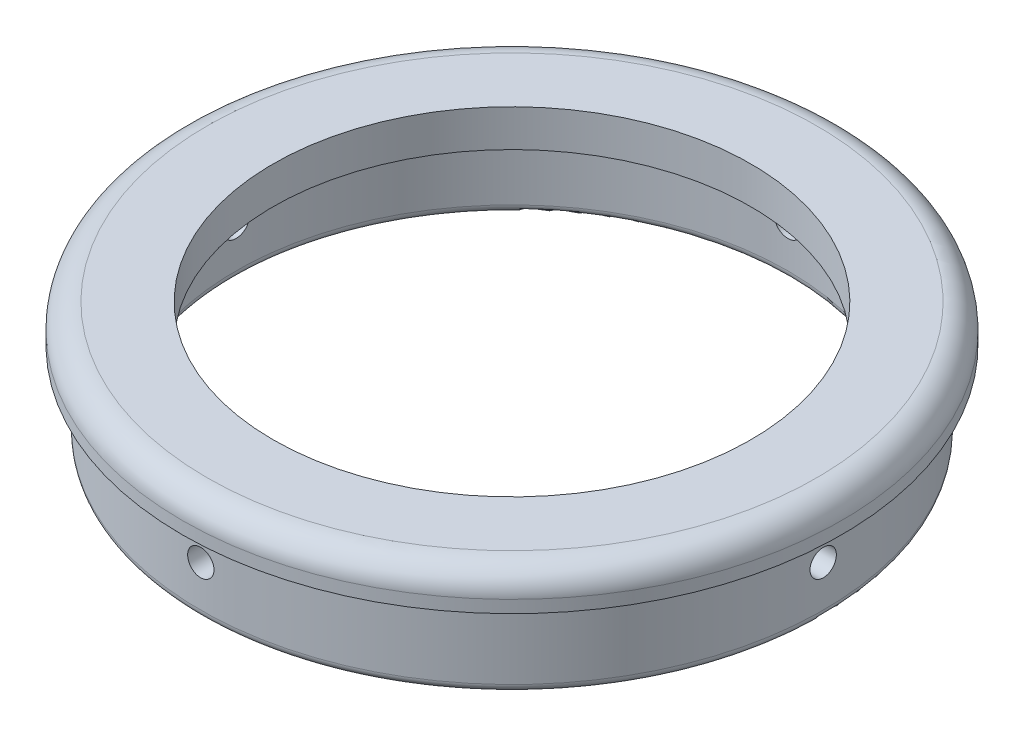
SolidWorks part; units mm, degrees
material "PA 类型 6"
ref_plane "前视基准面" through (0, 0, 0) normal (0, 0, 1) x (1, 0, 0)
ref_plane "上视基准面" through (0, 0, 0) normal (0, 1, 0) x (1, 0, 0)
ref_plane "右视基准面" through (0, 0, 0) normal (1, 0, 0) x (0, 0, -1)
other "Configuration Table"
sketch "草图1" plane through (0, 0, 0) normal (0, 1, 0) x (1, 0, 0)
  circle A0 centre (0, 0) radius 40
  circle A1 centre (0, 0) radius 29
extrude "凸台-拉伸1" add sketch "草图1" along normal blind 4.5
sketch "草图2" plane through (0, 0, 0) normal (0, -1, 0) x (1, 0, 0)
  circle A0 centre (0, 0) radius 37.8
  circle A1 centre (0, 0) radius 33.5
extrude "凸台-拉伸2" add sketch "草图2" along normal blind 10
fillet "圆角1" radius 1 2 edges at (0, -10, -33.5) (0, -10, -37.8)
fillet "圆角2" radius 3 1 edges at (0, 4.5, 40)
sketch "草图3" plane through (0, 0, 0) normal (1, 0, 0) x (0, 0, -1)
  line L0 (0, -10) -> (0, -4) construction
  line L1 (-36.8, -10) -> (36.8, -10) construction
  line L2 (0, 7.975) -> (0, -7.975) construction
  circle A0 centre (0, -4) radius 1.6
extrude "切除-拉伸1" cut sketch "草图3" against normal through all both and the other way through all
sketch "草图4" plane through (0, 0, 0) normal (0, 0, 1) x (1, 0, 0)
  line L0 (0, -10) -> (0, -4) construction
  line L1 (-36.8, -10) -> (36.8, -10) construction
  line L2 (0, -7.975) -> (0, 7.975) construction
  circle A0 centre (0, -4) radius 1.6
extrude "切除-拉伸2" cut sketch "草图4" against normal through all both and the other way through all
